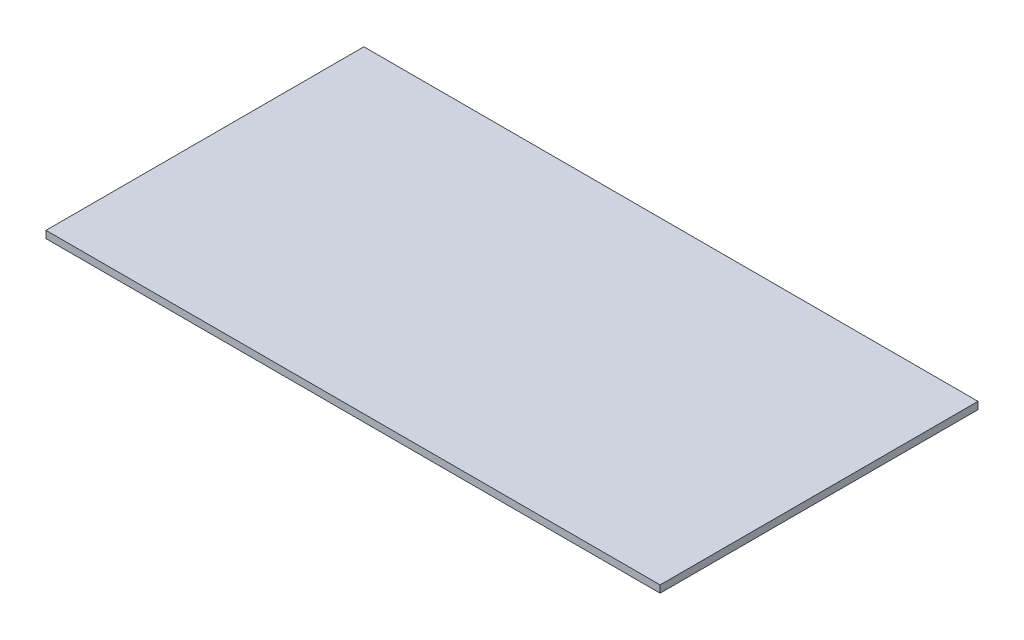
SolidWorks part; units mm, degrees
ref_plane "Front Plane" through (0, 0, 0) normal (0, 0, 1) x (1, 0, 0)
ref_plane "Top Plane" through (0, 0, 0) normal (0, 1, 0) x (1, 0, 0)
ref_plane "Right Plane" through (0, 0, 0) normal (1, 0, 0) x (0, 0, -1)
sketch "Sketch1" plane through (0, 0, 0) normal (0, 1, 0) x (1, 0, 0)
  line L1 (-43.5537, 5.4339) -> (41.4463, 5.4339)
  line L2 (-43.5537, 5.4339) -> (-43.5537, -38.5661)
  line L3 (-43.5537, -38.5661) -> (41.4463, -38.5661)
  line L4 (41.4463, 5.4339) -> (41.4463, -38.5661)
  dimension "D1" = 85
  dimension "D2" = 44
extrude "Boss-Extrude1" add sketch "Sketch1" along normal blind 1
